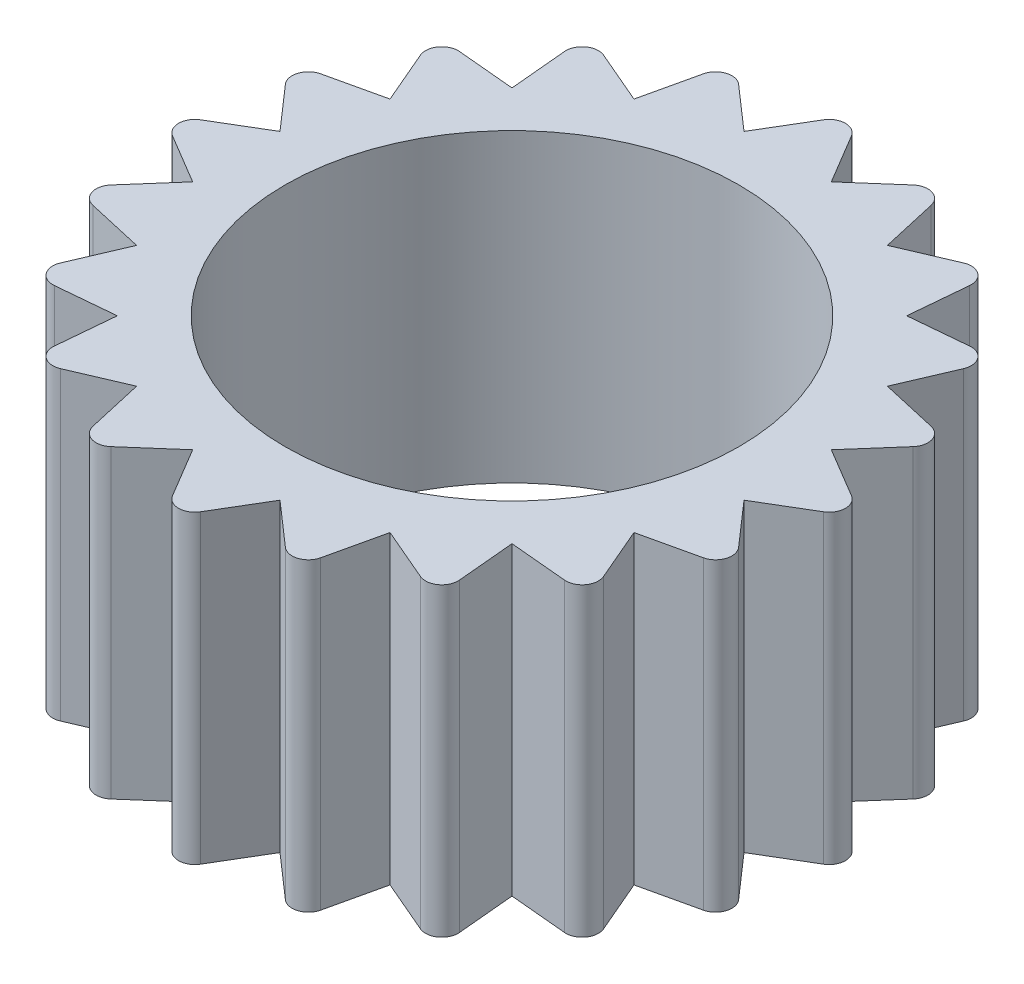
SolidWorks part; units mm, degrees
ref_plane "Front Plane" through (0, 0, 0) normal (0, 0, 1) x (1, 0, 0)
ref_plane "Top Plane" through (0, 0, 0) normal (0, 1, 0) x (1, 0, 0)
ref_plane "Right Plane" through (0, 0, 0) normal (1, 0, 0) x (0, 0, -1)
sketch "Sketch1" plane through (0, 0, 0) normal (0, 1, 0) x (1, 0, 0)
  line L1 (0, -55) -> (0, 55) construction
  line L4 (0, 17.15) -> (2.1459, 13.5486)
  line L99 (0, 17.15) -> (-2.1459, 13.5486)
  line L101 (5.2996, 16.3106) -> (2.1459, 13.5486)
  line L102 (5.2996, 16.3106) -> (6.2276, 12.2224)
  line L103 (10.0805, 13.8746) -> (6.2276, 12.2224)
  line L104 (10.0805, 13.8746) -> (9.6998, 9.6998)
  line L105 (13.8746, 10.0805) -> (9.6998, 9.6998)
  line L106 (13.8746, 10.0805) -> (12.2224, 6.2276)
  line L107 (16.3106, 5.2996) -> (12.2224, 6.2276)
  line L108 (16.3106, 5.2996) -> (13.5486, 2.1459)
  line L109 (17.15, 0) -> (13.5486, 2.1459)
  line L110 (17.15, 0) -> (13.5486, -2.1459)
  line L111 (16.3106, -5.2996) -> (13.5486, -2.1459)
  line L112 (16.3106, -5.2996) -> (12.2224, -6.2276)
  line L113 (13.8746, -10.0805) -> (12.2224, -6.2276)
  line L114 (13.8746, -10.0805) -> (9.6998, -9.6998)
  line L115 (10.0805, -13.8746) -> (9.6998, -9.6998)
  line L116 (10.0805, -13.8746) -> (6.2276, -12.2224)
  line L117 (5.2996, -16.3106) -> (6.2276, -12.2224)
  line L118 (5.2996, -16.3106) -> (2.1459, -13.5486)
  line L119 (0, -17.15) -> (2.1459, -13.5486)
  line L120 (0, -17.15) -> (-2.1459, -13.5486)
  line L121 (-5.2996, -16.3106) -> (-2.1459, -13.5486)
  line L122 (-5.2996, -16.3106) -> (-6.2276, -12.2224)
  line L123 (-10.0805, -13.8746) -> (-6.2276, -12.2224)
  line L124 (-10.0805, -13.8746) -> (-9.6998, -9.6998)
  line L125 (-13.8746, -10.0805) -> (-9.6998, -9.6998)
  line L126 (-13.8746, -10.0805) -> (-12.2224, -6.2276)
  line L127 (-16.3106, -5.2996) -> (-12.2224, -6.2276)
  line L128 (-16.3106, -5.2996) -> (-13.5486, -2.1459)
  line L129 (-17.15, 0) -> (-13.5486, -2.1459)
  line L130 (-17.15, 0) -> (-13.5486, 2.1459)
  line L131 (-16.3106, 5.2996) -> (-13.5486, 2.1459)
  line L132 (-16.3106, 5.2996) -> (-12.2224, 6.2276)
  line L133 (-13.8746, 10.0805) -> (-12.2224, 6.2276)
  line L134 (-13.8746, 10.0805) -> (-9.6998, 9.6998)
  line L135 (-10.0805, 13.8746) -> (-9.6998, 9.6998)
  line L136 (-10.0805, 13.8746) -> (-6.2276, 12.2224)
  line L137 (-5.2996, 16.3106) -> (-6.2276, 12.2224)
  line L138 (-5.2996, 16.3106) -> (-2.1459, 13.5486)
  circle A0 centre (0, 0) radius 11.15
  point P57 (0, 0)
  point P69 (0, 0)
  point P105 (0, 0)
  dimension "D1" = 22.3
  dimension "D4" = 20
extrude "Boss-Extrude1" add sketch "Sketch1" along normal blind 15
fillet "Fillet3" radius 0.8 20 edges at (16.3106, 7.5, 5.2996) (17.15, 7.5, 0) (-5.2996, 7.5, -16.3106) (16.3106, 7.5, -5.2996) (13.8746, 7.5, -10.0805) (10.0805, 7.5, -13.8746) (5.2996, 7.5, -16.3106) (0, 7.5, -17.15) (-10.0805, 7.5, -13.8746) (-13.8746, 7.5, -10.0805) (-16.3106, 7.5, -5.2996) (-17.15, 7.5, 0) (-16.3106, 7.5, 5.2996) (13.8746, 7.5, 10.0805) (10.0805, 7.5, 13.8746) (5.2996, 7.5, 16.3106) (0, 7.5, 17.15) (-13.8746, 7.5, 10.0805) (-10.0805, 7.5, 13.8746) (-5.2996, 7.5, 16.3106)
